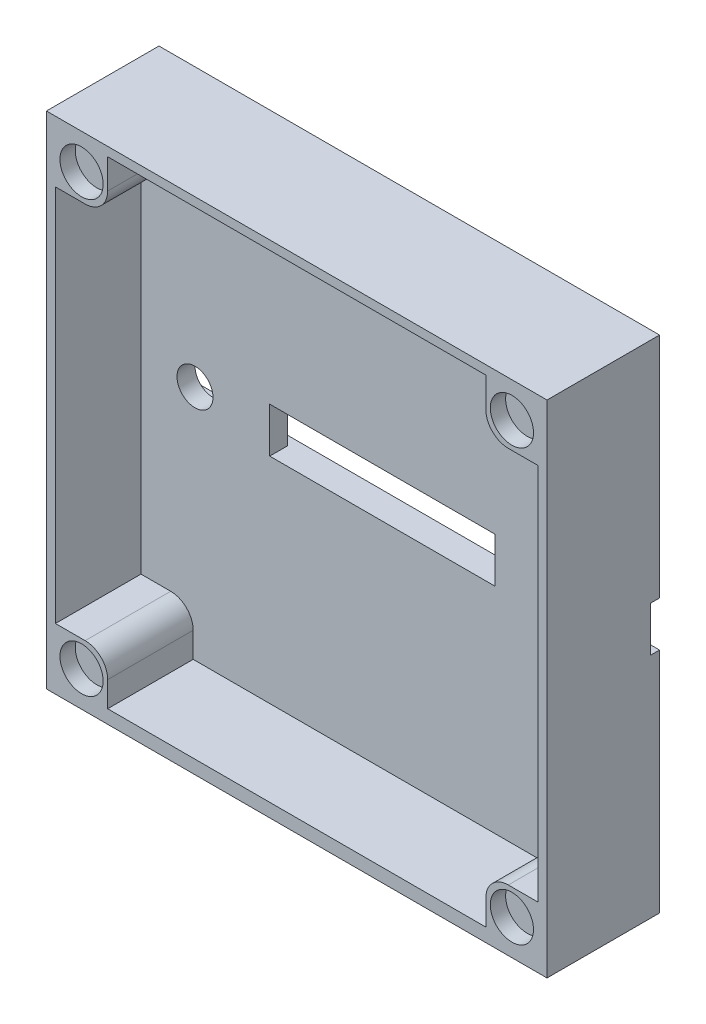
SolidWorks part; units mm, degrees
ref_plane "Přední rovina" through (0, 0, 0) normal (0, 0, 1) x (1, 0, 0)
ref_plane "Horní rovina" through (0, 0, 0) normal (0, 1, 0) x (1, 0, 0)
ref_plane "Pravá rovina" through (0, 0, 0) normal (1, 0, 0) x (0, 0, -1)
sketch "Skica1" plane through (0, 0, 0) normal (0, 0, 1) x (1, 0, 0)
  line L1 (27.8, 27.8) -> (-27.8, 27.8)
  line L2 (27.8, 27.8) -> (27.8, -27.8)
  line L3 (27.8, -27.8) -> (-27.8, -27.8)
  line L4 (-27.8, 27.8) -> (-27.8, -27.8)
  line L5 (27.8, 27.8) -> (-27.8, -27.8) construction
  line L6 (27.8, -27.8) -> (-27.8, 27.8) construction
  point P0 (0, 0)
  point P5 (-27.5, 0)
  point P11 (4.5, 0)
  dimension "D1" = 55.6
  dimension "D2" = 55.6
extrude "Přidat vysunutím2" add sketch "Skica1" along normal blind 3 contours L2 L1 L4 L3
sketch "Skica4" plane through (0, 0, 3) normal (0, 0, 1) x (1, 0, 0)
  line L1 (-12.5, 2.5) -> (12.5, 2.5)
  line L2 (-12.5, 2.5) -> (-12.5, -2.5)
  line L3 (-12.5, -2.5) -> (12.5, -2.5)
  line L4 (12.5, 2.5) -> (12.5, -2.5)
  line L5 (-12.5, 2.5) -> (12.5, -2.5) construction
  line L6 (-12.5, -2.5) -> (12.5, 2.5) construction
  line L10 (-27.8, 27.8) -> (-27.8, -27.8) construction
  point P0 (0, 0)
  dimension "D1" = 5
  dimension "D2" = 25
  dimension "D3" = 15.3
extrude "Odebrat vysunutím1" cut sketch "Skica4" against normal blind 2
sketch "Skica5" plane through (0, 0, 0) normal (0, 0, -1) x (-1, 0, 0)
  line L10 (27.8, 27.8) -> (27.8, -27.8) construction
  line L11 (-27.8, 2.5) -> (27.8, 2.5)
  line L12 (-27.8, 2.5) -> (-27.8, -2.5)
  line L13 (-27.8, -2.5) -> (27.8, -2.5)
  line L14 (27.8, 2.5) -> (27.8, -2.5)
  line L15 (-27.8, 2.5) -> (27.8, -2.5) construction
  line L16 (-27.8, -2.5) -> (27.8, 2.5) construction
  point P0 (0, 0)
  dimension "D1" = 5
extrude "Odebrat vysunutím3" cut sketch "Skica5" against normal blind 1 contours L11 L14 L13 L12
sketch "Skica14" plane through (0, 0, 3) normal (0, 0, 1) x (1, 0, 0)
  line L1 (-27.8, 27.8) -> (27.8, 27.8)
  line L2 (-27.8, 27.8) -> (-27.8, -27.8)
  line L3 (-27.8, -27.8) -> (27.8, -27.8)
  line L4 (27.8, 27.8) -> (27.8, -27.8)
  line L5 (-26.8, 26.8) -> (26.8, 26.8)
  line L6 (-26.8, 26.8) -> (-26.8, -27.8)
  line L7 (-26.8, -27.8) -> (26.8, -27.8)
  line L8 (26.8, 26.8) -> (26.8, -27.8)
  line L9 (-26.8, -27.8) -> (26.8, -27.8)
  line L10 (-26.8, -27.8) -> (-26.8, -26.8)
  line L12 (26.8, -27.8) -> (26.8, -26.3)
  line L13 (-26.8, -27.8) -> (26.8, -27.8)
  line L14 (-26.8, -27.8) -> (-26.8, -26.3)
  line L15 (-26.8, -26.3) -> (26.8, -26.3)
  line L16 (26.8, -27.8) -> (26.8, -26.3)
  line M13 (-27.8, -27.8) -> (27.8, -27.8)
  line M14 (27.8, -27.8) -> (27.8, 27.8)
  line M15 (27.8, 27.8) -> (-27.8, 27.8)
  line M16 (-27.8, 27.8) -> (-27.8, -27.8)
  dimension "D1" = 1
  dimension "D2" = 1
  dimension "D3" = 1
  dimension "D4" = 0
  dimension "D5" = 1
  dimension "D6" = 53.6
extrude "Přidat vysunutím9" add sketch "Skica14" along normal blind 9.5 contours L5 L8 L6 M13 M14 M15 M16 | L14 L13 L16 L15
sketch "Skica17" plane through (0, 0, 1) normal (0, 0, -1) x (-1, 0, 0)
  line L0 (-27.8, 2.5) -> (-27.8, -2.5) construction
  line L1 (-12.5, -2.5) -> (-12.5, 2.5) construction
  line L2 (27.8, 2.5) -> (27.8, -2.5) construction
  circle A0 centre (-20.8, 0) radius 2
  circle A1 centre (20.8, 0) radius 2
  dimension "D1" = 4
  dimension "D2" = 4
  dimension "D3" = 7
  dimension "D4" = 8.3
  dimension "D5" = 7
extrude "Odebrat vysunutím8" cut sketch "Skica17" against normal blind 4
sketch "Skica19" plane through (0, 0, 0) normal (0, 0, -1) x (-1, 0, 0)
  line L1 (-27.8, 27.8) -> (-21, 27.8)
  line L2 (-27.8, 27.8) -> (-27.8, 21)
  line L3 (-27.8, 21) -> (-21, 21)
  line L4 (-21, 27.8) -> (-21, 21)
  line L5 (27.8, 27.8) -> (21, 27.8)
  line L6 (27.8, 27.8) -> (27.8, 21)
  line L7 (27.8, 21) -> (21, 21)
  line L8 (21, 27.8) -> (21, 21)
  line L9 (-27.8, -27.8) -> (-21, -27.8)
  line L10 (-27.8, -27.8) -> (-27.8, -21)
  line L11 (-27.8, -21) -> (-21, -21)
  line L12 (-21, -27.8) -> (-21, -21)
  line L13 (27.8, -27.8) -> (21, -27.8)
  line L14 (27.8, -27.8) -> (27.8, -21)
  line L15 (27.8, -21) -> (21, -21)
  line L16 (21, -27.8) -> (21, -21)
  dimension "D1" = 6.8
  dimension "D2" = 6.8
  dimension "D3" = 6.8
  dimension "D4" = 6.8
extrude "Přidat vysunutím10" add sketch "Skica19" against normal blind 12.5
sketch "Skica20" plane through (0, 0, 12.5) normal (0, 0, 1) x (1, 0, 0)
  line L0 (-27.8, -27.8) -> (27.8, -27.8) construction
  line L2 (-27.8, 27.8) -> (-27.8, -27.8) construction
  line L3 (27.8, 27.8) -> (-27.8, 27.8) construction
  line L4 (27.8, -27.8) -> (27.8, 27.8) construction
  line L5 (-27.8, -27.8) -> (27.8, -27.8) construction
  circle A0 centre (-23.9, -23.9) radius 2.4
  circle A1 centre (-23.9, 23.9) radius 2.4
  circle A2 centre (23.9003, 23.9) radius 2.4
  circle A3 centre (23.9003, -23.9) radius 2.4
  dimension "D1" = 4.8
  dimension "D4" = 4.8
  dimension "D5" = 3.9
  dimension "D7" = 4.8
  dimension "D10" = 4.8
  dimension "D2" = 3.9
  dimension "D3" = 3.9
  dimension "D6" = 3.9
  dimension "D8" = 3.8997
  dimension "D9" = 3.9
  dimension "D11" = 3.9
  dimension "D12" = 3.8997
extrude "Odebrat vysunutím9" cut sketch "Skica20" against normal blind 1.7
fillet "Zaoblit1" radius 2.5 4 edges at (21, 21, 7.75) (21, -21, 7.75) (-21, -21, 7.75) (-21, 21, 7.75)
